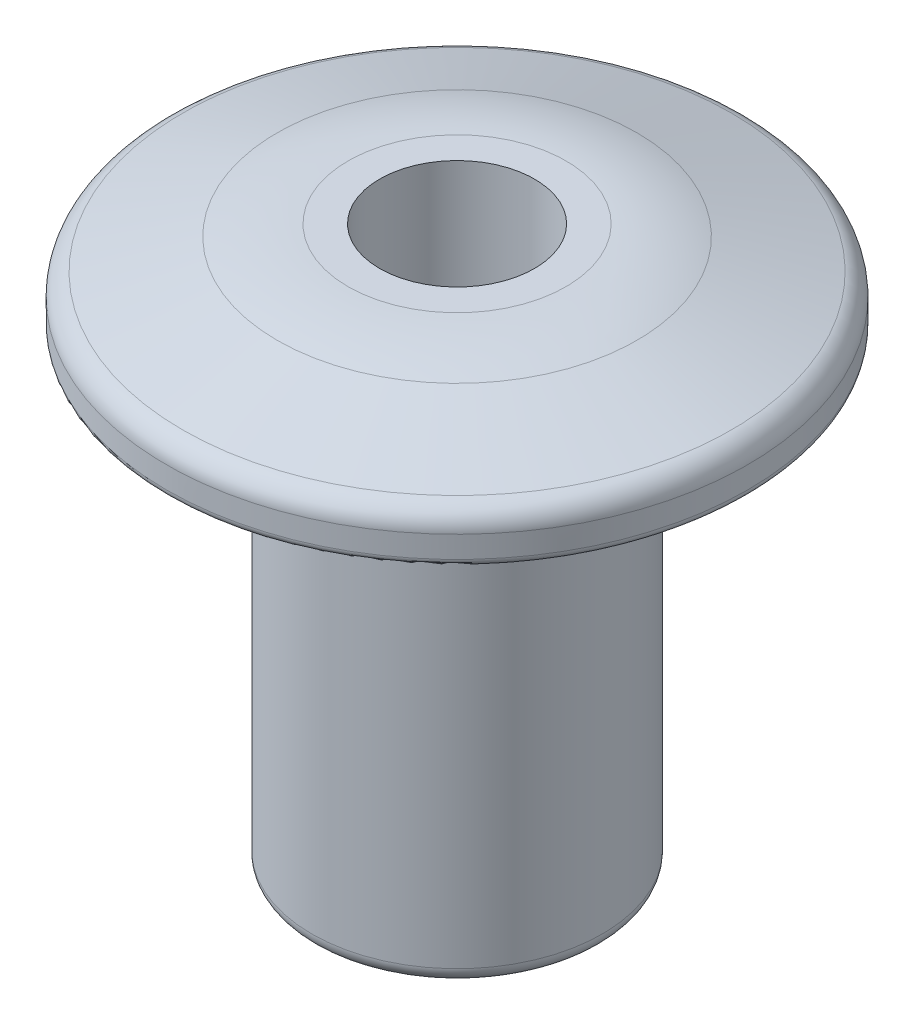
SolidWorks part; units mm, degrees
ref_plane "Front Plane" through (0, 0, 0) normal (0, 0, 1) x (1, 0, 0)
ref_plane "Top Plane" through (0, 0, 0) normal (0, 1, 0) x (1, 0, 0)
ref_plane "Right Plane" through (0, 0, 0) normal (1, 0, 0) x (0, 0, -1)
sketch "Sketch1" plane through (0, 0, 0) normal (0, 1, 0) x (1, 0, 0)
  circle A0 centre (0, 0) radius 2.3813
  dimension "D1" = 4.7625
extrude "Boss-Extrude1" add sketch "Sketch1" along normal blind 7.62
sketch "Sketch2" plane through (0, 7.62, 0) normal (0, 1, 0) x (1, 0, 0)
  circle A0 centre (0, 0) radius 4.7625
  dimension "D1" = 9.525
extrude "Boss-Extrude2" add sketch "Sketch2" along normal blind 1.524
fillet "Fillet1" radius 0.254 1 edges at (0, 0, 2.3813)
sketch "Sketch3" plane through (0, 0, 0) normal (1, 0, 0) x (0, 0, -1)
  line L0 (0, 9.144) -> (0, 0) construction
  line L1 (4.7625, 9.144) -> (-4.7625, 9.144) construction
  line L2 (-2.3813, 9.144) -> (-4.7625, 8.382)
  line L3 (-4.7625, 9.144) -> (-4.7625, 7.62) construction
  line L4 (-4.7625, 8.382) -> (-4.7625, 9.144)
  line L5 (-4.7625, 9.144) -> (-2.3813, 9.144)
  line L6 (-2.3813, 7.62) -> (-2.3813, 0.254) construction
  dimension "D1" = 0.762
revolve "Cut-Revolve1" cut sketch "Sketch3" angle 360 about L0
fillet "Fillet2" radius 0.381 1 edges at (0, 8.382, 4.7625)
fillet "Fillet3" radius 0.127 1 edges at (0, 7.62, 4.7625)
fillet "Fillet4" radius 3.81 1 edges at (0, 9.144, 2.3813)
sketch "Sketch4" plane through (0, 9.144, 0) normal (0, 1, 0) x (1, 0, 0)
  circle A0 centre (0, 0) radius 1.27
  dimension "D1" = 2.54
extrude "Cut-Extrude1" cut sketch "Sketch4" against normal blind 2.54
fillet "Fillet5" radius 0.635 1 edges at (0, 6.604, 1.27)
